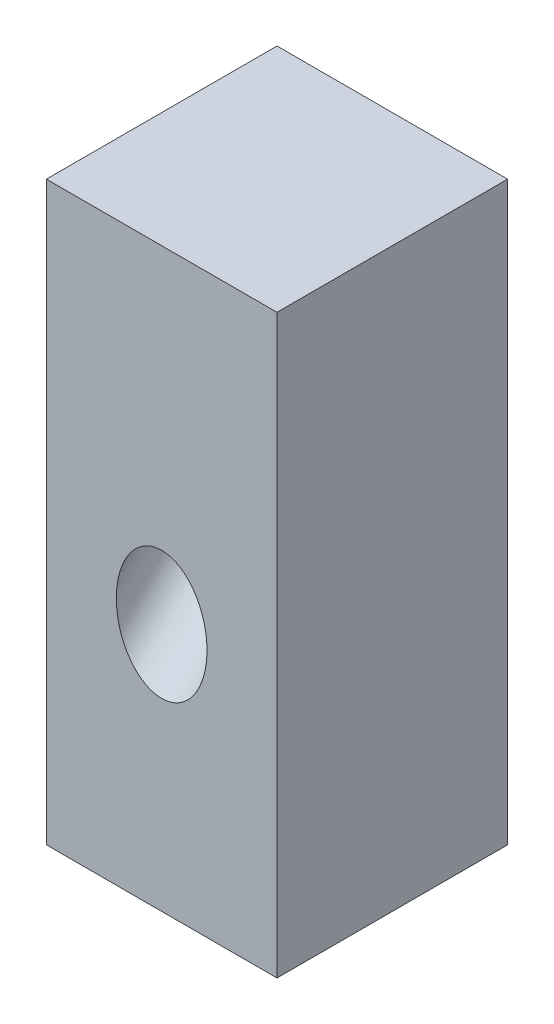
SolidWorks part; units mm, degrees
material "Polyurethane Foam Rigid"
ref_plane "Front Plane" through (0, 0, 0) normal (0, 0, 1) x (1, 0, 0)
ref_plane "Top Plane" through (0, 0, 0) normal (0, 1, 0) x (1, 0, 0)
ref_plane "Right Plane" through (0, 0, 0) normal (1, 0, 0) x (0, 0, -1)
sketch "Sketch1" plane through (0, 0, 0) normal (0, 1, 0) x (1, 0, 0)
  line L1 (0, 0) -> (40, 0)
  line L2 (0, 0) -> (0, 40)
  line L3 (0, 40) -> (40, 40)
  line L4 (40, 0) -> (40, 40)
  dimension "D1" = 40
  dimension "D2" = 40
extrude "Boss-Extrude1" add sketch "Sketch1" along normal blind 68 and the other way blind 32
sketch "Sketch3" plane through (0, 0, 0) normal (0, 0, 1) x (1, 0, 0)
  line L0 (0, 0) -> (40, 0) construction
  line L1 (40, -32) -> (40, 68) construction
ref_plane "Plane1" through (0, 0, 0) normal (0, -0.7071, 0.7071) x (1, 0, 0)
sketch "Sketch4" plane through (0, 0, 0) normal (0, -0.7071, 0.7071) x (1, 0, 0)
  line L1 (0, 0) -> (40, 0) construction
  circle A0 centre (20, 7.825) radius 7.825
  point P5 (20, 0.2788)
  dimension "D1" = 15.65
extrude "Cut-Extrude2" cut sketch "Sketch4" against normal through all draft 0.28 contours A0 draft outward yes
